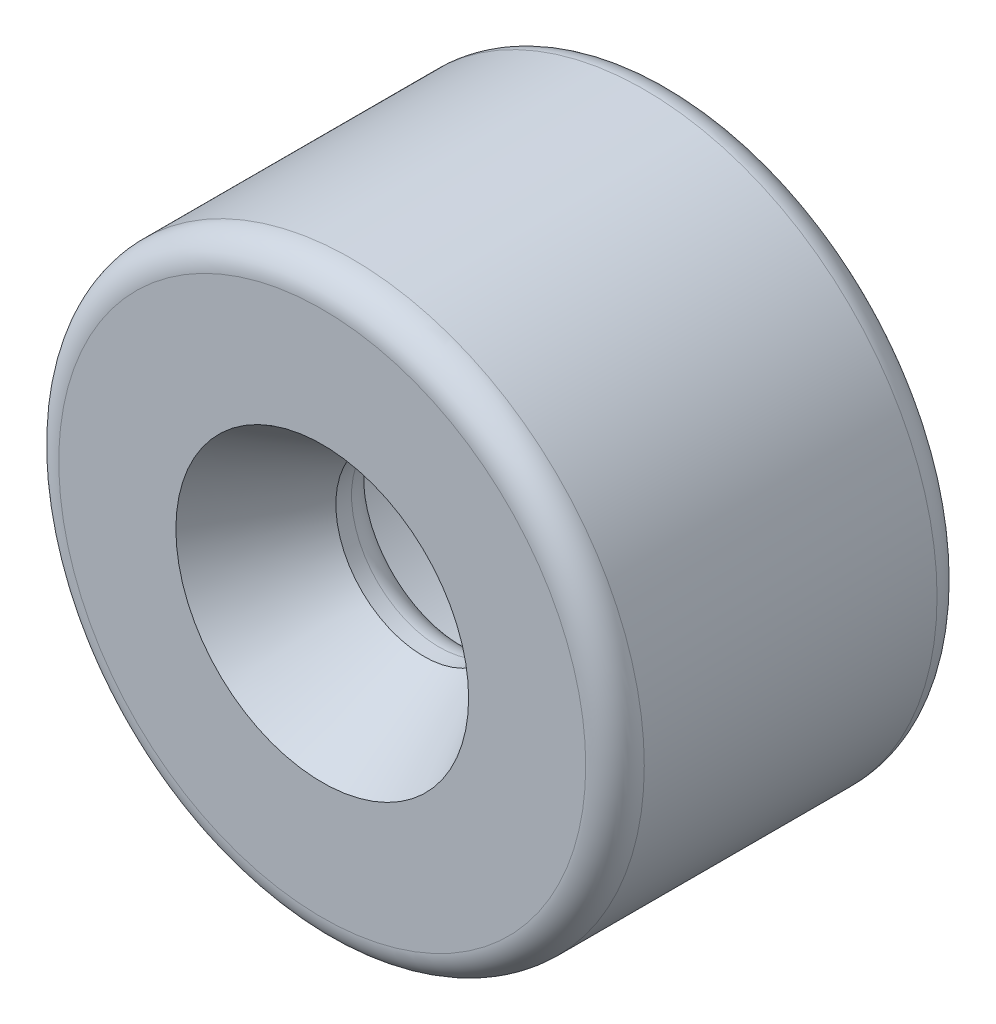
SolidWorks part; units mm, degrees
ref_plane "Front Plane" through (0, 0, 0) normal (0, 0, 1) x (1, 0, 0)
ref_plane "Top Plane" through (0, 0, 0) normal (0, 1, 0) x (1, 0, 0)
ref_plane "Right Plane" through (0, 0, 0) normal (1, 0, 0) x (0, 0, -1)
sketch "Sketch1" plane through (0, 0, 0) normal (0, 0, 1) x (1, 0, 0)
  circle A0 centre (0, 0) radius 5
  circle A1 centre (0, 0) radius 1.5
  dimension "D1" = 10
  dimension "D2" = 3
extrude "Boss-Extrude1" add sketch "Sketch1" along normal blind 6
sketch "Sketch2" plane through (0, 0, 0) normal (0, 0, 1) x (1, 0, 0)
  circle A0 centre (0, 0) radius 3.75
  dimension "D1" = 7.5
extrude "Cut-Extrude1" cut sketch "Sketch2" along normal blind 3.5
fillet "Fillet1" radius 0.5 4 edges at (5, 0, 0) (3.75, 0, 0) (1.5, 0, 3.5) (5, 0, 6)
chamfer "Chamfer1" distance 1 angle 60 1 edges at (1.5, 0, 6)
